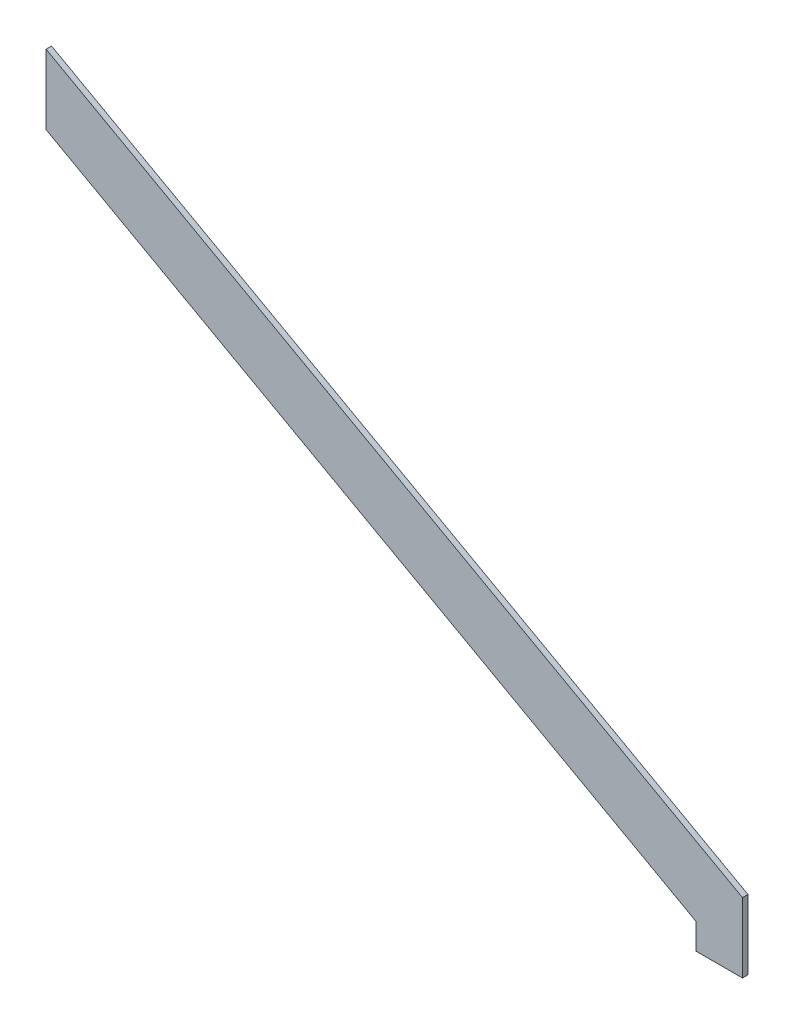
SolidWorks part; units mm, degrees
ref_plane "Front Plane" through (0, 0, 0) normal (0, 0, 1) x (1, 0, 0)
ref_plane "Top Plane" through (0, 0, 0) normal (0, 1, 0) x (1, 0, 0)
ref_plane "Right Plane" through (0, 0, 0) normal (1, 0, 0) x (0, 0, -1)
sketch "Sketch1" plane through (0, 0, 0) normal (0, 0, 1) x (1, 0, 0)
  line L0 (-381, 211.4611) -> (0, 0)
  line L1 (0, 0) -> (0, 38.1)
  line L3 (0, 38.1) -> (-381, 249.5611)
  line L5 (-381, 249.5611) -> (-381, 211.4611)
  dimension "D1" = 38.1
  dimension "D2" = 381
  dimension "D3" = 435.7486
extrude "Boss-Extrude1" add sketch "Sketch1" along normal blind 3
sketch "Sketch3" plane through (0, 0, 3) normal (0, 0, 1) x (1, 0, 0)
  line L0 (0, 0) -> (-25.4, 0)
  line L1 (-25.4, 0) -> (-25.4, 14.0974)
  line L2 (-381, 211.4611) -> (0, 0) construction
  line L3 (-25.4, 14.0974) -> (0, 0)
  dimension "D1" = 25.4
extrude "Boss-Extrude2" add sketch "Sketch3" against normal up to surface (3 mm away) up to face at (-190.5, 124.7806, 0)
